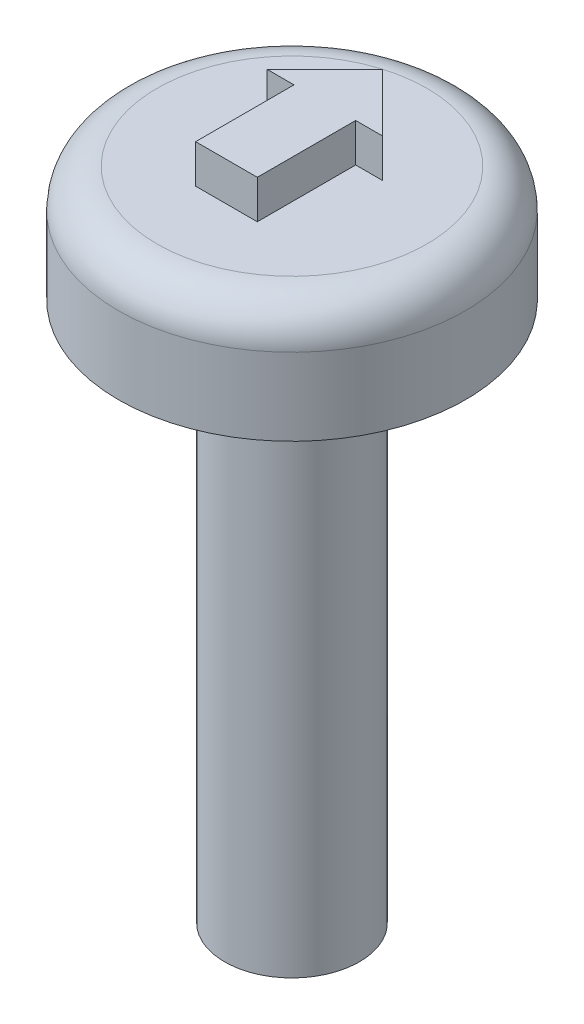
SolidWorks part; units mm, degrees
ref_plane "Front Plane" through (0, 0, 0) normal (0, 0, 1) x (1, 0, 0)
ref_plane "Top Plane" through (0, 0, 0) normal (0, 1, 0) x (1, 0, 0)
ref_plane "Right Plane" through (0, 0, 0) normal (1, 0, 0) x (0, 0, -1)
ref_plane "Plane1" through (0, 115.6015, 0) normal (0, 1, 0) x (1, 0, 0)
sketch "Sketch1" plane through (0, 115.6015, 0) normal (0, 1, 0) x (1, 0, 0)
  circle A0 centre (40.9103, -143.1552) radius 4.5
  dimension "D1" = 9
extrude "Boss-Extrude1" add sketch "Sketch1" along normal blind 3
fillet "Fillet1" radius 1 1 edges at (40.9103, 118.6015, 147.6551)
sketch "Sketch2" plane through (0, 118.6015, 0) normal (0, 1, 0) x (1, 0, 0)
  line L0 (40.1103, -142.3033) -> (40.1103, -144.8552)
  line L1 (40.1103, -144.8552) -> (41.7103, -144.8552)
  line L2 (41.7103, -144.8552) -> (41.7103, -142.3033)
  line L3 (41.7103, -142.3033) -> (42.4103, -142.3033)
  line L4 (42.4103, -142.3033) -> (40.9103, -140.8033)
  line L5 (40.9103, -140.8033) -> (39.4103, -142.3033)
  line L6 (39.4103, -142.3033) -> (40.1103, -142.3033)
  point P0 (40.9103, -143.1552)
  dimension "D1" = 0.8
  dimension "D2" = 0.8
  dimension "D3" = 1.7
  dimension "D4" = 0.7
  dimension "D5" = 0.7
  dimension "D6" = 2.3519
  dimension "D7" = 45
extrude "Boss-Extrude2" add sketch "Sketch2" along normal blind 1
ref_plane "Plane3" through (0, 115.6015, 0) normal (0, -1, 0) x (-1, 0, 0)
sketch "Sketch6" plane through (0, 115.6015, 0) normal (0, -1, 0) x (-1, 0, 0)
  circle A0 centre (-40.9103, -143.1552) radius 4.5 construction
  circle A1 centre (-40.9103, -143.1552) radius 4.5 construction
  circle A2 centre (-40.9103, -143.1552) radius 1.75
  dimension "D1" = 3.5
extrude "Boss-Extrude3" add sketch "Sketch6" along normal blind 14
